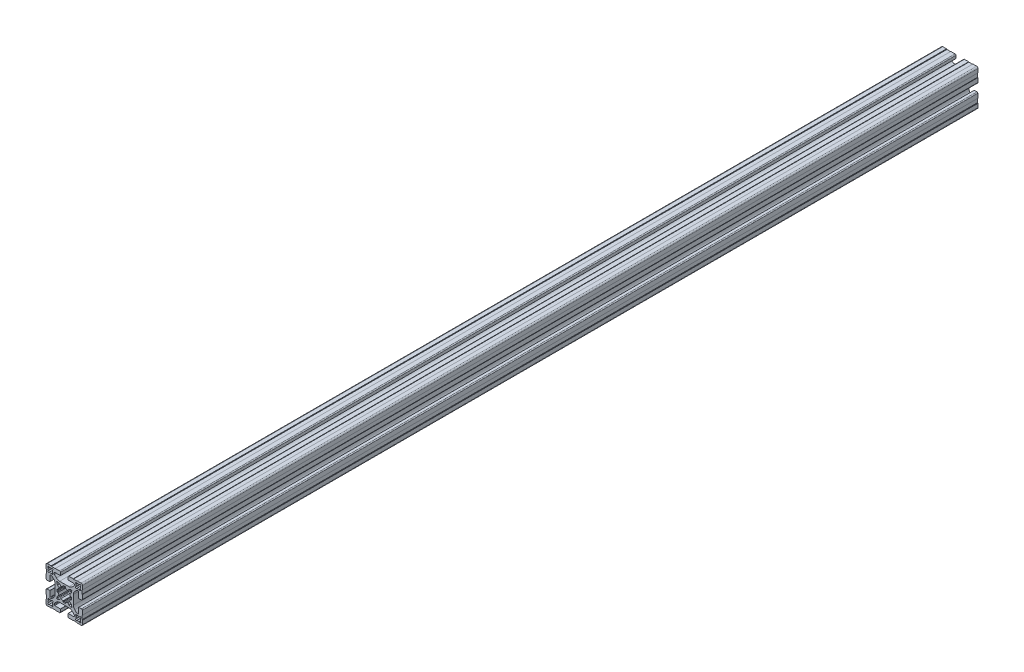
SolidWorks part; units mm, degrees
other "Item de detalhe1"
other "Item de detalhe2"
material "6063-T5"
ref_plane "Plano frontal" through (0, 0, 0) normal (0, 0, 1) x (1, 0, 0)
ref_plane "Plano superior" through (0, 0, 0) normal (0, 1, 0) x (1, 0, 0)
ref_plane "Plano direito" through (0, 0, 0) normal (1, 0, 0) x (0, 0, -1)
sketch "Esboço1" plane through (0, 0, 0) normal (0, 0, 1) x (1, 0, 0)
  point P0 (0, 0)
  line B0 (-5.3139, -7.6355) -> (-7.6488, -8.2611)
  arc B1 (-8.2611, -7.6488) -> (-7.6488, -8.2611) centre (-7.7782, -7.7782) ccw
  line B2 (-8.2611, -7.6488) -> (-7.6355, -5.3139)
  arc B3 (-7.4569, -5.0466) -> (-7.6355, -5.3139) centre (-7.1525, -5.4433) ccw
  line B4 (-7.4569, -5.0466) -> (-5.744, -3.7322)
  arc B5 (-6.7007, -1.4225) -> (-5.744, -3.7322) centre (0, 0) ccw
  line B6 (-6.7007, -1.4225) -> (-7.5204, -1.3146)
  arc B7 (-7.9522, -0.8735) -> (-7.5204, -1.3146) centre (-7.4552, -0.8189) ccw
  arc B8 (-7.9522, 0.8735) -> (-7.9522, -0.8735) centre (0, 0) ccw
  arc B9 (-7.5204, 1.3146) -> (-7.9522, 0.8735) centre (-7.4552, 0.8189) ccw
  line B10 (-7.5204, 1.3146) -> (-6.7007, 1.4225)
  arc B11 (-5.744, 3.7322) -> (-6.7007, 1.4225) centre (0, 0) ccw
  line B12 (-5.744, 3.7322) -> (-7.4569, 5.0466)
  arc B13 (-7.6355, 5.3139) -> (-7.4569, 5.0466) centre (-7.1525, 5.4433) ccw
  line B14 (-7.6355, 5.3139) -> (-8.2611, 7.6488)
  arc B15 (-7.6488, 8.2611) -> (-8.2611, 7.6488) centre (-7.7782, 7.7782) ccw
  line B16 (-7.6488, 8.2611) -> (-5.3139, 7.6355)
  arc B17 (-5.0466, 7.4569) -> (-5.3139, 7.6355) centre (-5.4433, 7.1525) ccw
  line B18 (-5.0466, 7.4569) -> (-3.7322, 5.744)
  arc B19 (-1.4225, 6.7007) -> (-3.7322, 5.744) centre (0, 0) ccw
  line B20 (-1.4225, 6.7007) -> (-1.3146, 7.5204)
  arc B21 (-0.8735, 7.9522) -> (-1.3146, 7.5204) centre (-0.8189, 7.4552) ccw
  arc B22 (0.8735, 7.9522) -> (-0.8735, 7.9522) centre (0, 0) ccw
  arc B23 (1.3146, 7.5204) -> (0.8735, 7.9522) centre (0.8189, 7.4552) ccw
  line B24 (1.3146, 7.5204) -> (1.4225, 6.7007)
  arc B25 (3.7322, 5.744) -> (1.4225, 6.7007) centre (0, 0) ccw
  line B26 (3.7322, 5.744) -> (5.0466, 7.4569)
  arc B27 (5.3139, 7.6355) -> (5.0466, 7.4569) centre (5.4433, 7.1525) ccw
  line B28 (5.3139, 7.6355) -> (7.6488, 8.2611)
  arc B29 (8.2611, 7.6488) -> (7.6488, 8.2611) centre (7.7782, 7.7782) ccw
  line B30 (8.2611, 7.6488) -> (7.6355, 5.3139)
  arc B31 (7.4569, 5.0466) -> (7.6355, 5.3139) centre (7.1525, 5.4433) ccw
  line B32 (7.4569, 5.0466) -> (5.744, 3.7322)
  arc B33 (6.7007, 1.4225) -> (5.744, 3.7322) centre (0, 0) ccw
  line B34 (6.7007, 1.4225) -> (7.5204, 1.3146)
  arc B35 (7.9522, 0.8735) -> (7.5204, 1.3146) centre (7.4552, 0.8189) ccw
  arc B36 (7.9522, -0.8735) -> (7.9522, 0.8735) centre (0, 0) ccw
  arc B37 (7.5204, -1.3146) -> (7.9522, -0.8735) centre (7.4552, -0.8189) ccw
  line B38 (7.5204, -1.3146) -> (6.7007, -1.4225)
  arc B39 (5.744, -3.7322) -> (6.7007, -1.4225) centre (0, 0) ccw
  line B40 (5.744, -3.7322) -> (7.4569, -5.0466)
  arc B41 (7.6355, -5.3139) -> (7.4569, -5.0466) centre (7.1525, -5.4433) ccw
  line B42 (7.6355, -5.3139) -> (8.2611, -7.6488)
  arc B43 (7.6488, -8.2611) -> (8.2611, -7.6488) centre (7.7782, -7.7782) ccw
  line B44 (7.6488, -8.2611) -> (5.3139, -7.6355)
  arc B45 (5.0466, -7.4569) -> (5.3139, -7.6355) centre (5.4433, -7.1525) ccw
  line B46 (5.0466, -7.4569) -> (3.7322, -5.744)
  arc B47 (1.4225, -6.7007) -> (3.7322, -5.744) centre (0, 0) ccw
  line B48 (1.4225, -6.7007) -> (1.3146, -7.5204)
  arc B49 (0.8735, -7.9522) -> (1.3146, -7.5204) centre (0.8189, -7.4552) ccw
  arc B50 (-0.8735, -7.9522) -> (0.8735, -7.9522) centre (0, 0) ccw
  arc B51 (-1.3146, -7.5204) -> (-0.8735, -7.9522) centre (-0.8189, -7.4552) ccw
  line B52 (-1.3146, -7.5204) -> (-1.4225, -6.7007)
  arc B53 (-3.7322, -5.744) -> (-1.4225, -6.7007) centre (0, 0) ccw
  line B54 (-3.7322, -5.744) -> (-5.0466, -7.4569)
  arc B55 (-5.3139, -7.6355) -> (-5.0466, -7.4569) centre (-5.4433, -7.1525) ccw
  line B56 (21, 0) -> (-21, 0) construction
  line B57 (-17.8572, 16.7966) -> (-17.4167, 16.356)
  arc B58 (-16.7966, 17.8572) -> (-17.8572, 16.7966) centre (-17.3269, 17.3269) ccw
  line B59 (-16.356, 17.4167) -> (-16.7966, 17.8572)
  arc B60 (-14.044, 17.4167) -> (-16.356, 17.4167) centre (-15.2, 15.2) ccw
  line B61 (-13.6034, 17.8572) -> (-14.044, 17.4167)
  arc B62 (-12.5428, 16.7966) -> (-13.6034, 17.8572) centre (-13.0731, 17.3269) ccw
  line B63 (-12.9833, 16.356) -> (-12.5428, 16.7966)
  arc B64 (-12.9833, 14.044) -> (-12.9833, 16.356) centre (-15.2, 15.2) ccw
  line B65 (-12.5428, 13.6034) -> (-12.9833, 14.044)
  arc B66 (-13.6034, 12.5428) -> (-12.5428, 13.6034) centre (-13.0731, 13.0731) ccw
  line B67 (-14.044, 12.9833) -> (-13.6034, 12.5428)
  arc B68 (-16.356, 12.9833) -> (-14.044, 12.9833) centre (-15.2, 15.2) ccw
  line B69 (-16.7966, 12.5428) -> (-16.356, 12.9833)
  arc B70 (-17.8572, 13.6034) -> (-16.7966, 12.5428) centre (-17.3269, 13.0731) ccw
  line B71 (-17.4167, 14.044) -> (-17.8572, 13.6034)
  arc B72 (-17.4167, 16.356) -> (-17.4167, 14.044) centre (-15.2, 15.2) ccw
  line B73 (17.4167, 14.044) -> (17.8572, 13.6034)
  arc B74 (16.7966, 12.5428) -> (17.8572, 13.6034) centre (17.3269, 13.0731) ccw
  line B75 (16.7966, 12.5428) -> (16.356, 12.9833)
  arc B76 (14.044, 12.9833) -> (16.356, 12.9833) centre (15.2, 15.2) ccw
  line B77 (14.044, 12.9833) -> (13.6034, 12.5428)
  arc B78 (12.5428, 13.6034) -> (13.6034, 12.5428) centre (13.0731, 13.0731) ccw
  line B79 (12.5428, 13.6034) -> (12.9833, 14.044)
  arc B80 (12.9833, 16.356) -> (12.9833, 14.044) centre (15.2, 15.2) ccw
  line B81 (12.9833, 16.356) -> (12.5428, 16.7966)
  arc B82 (13.6034, 17.8572) -> (12.5428, 16.7966) centre (13.0731, 17.3269) ccw
  line B83 (13.6034, 17.8572) -> (14.044, 17.4167)
  arc B84 (16.356, 17.4167) -> (14.044, 17.4167) centre (15.2, 15.2) ccw
  line B85 (16.356, 17.4167) -> (16.7966, 17.8572)
  arc B86 (17.8572, 16.7966) -> (16.7966, 17.8572) centre (17.3269, 17.3269) ccw
  line B87 (17.8572, 16.7966) -> (17.4167, 16.356)
  arc B88 (17.4167, 14.044) -> (17.4167, 16.356) centre (15.2, 15.2) ccw
  line B89 (-17.4167, -14.044) -> (-17.8572, -13.6034)
  arc B90 (-16.7966, -12.5428) -> (-17.8572, -13.6034) centre (-17.3269, -13.0731) ccw
  line B91 (-16.7966, -12.5428) -> (-16.356, -12.9833)
  arc B92 (-14.044, -12.9833) -> (-16.356, -12.9833) centre (-15.2, -15.2) ccw
  line B93 (-14.044, -12.9833) -> (-13.6034, -12.5428)
  arc B94 (-12.5428, -13.6034) -> (-13.6034, -12.5428) centre (-13.0731, -13.0731) ccw
  line B95 (-12.5428, -13.6034) -> (-12.9833, -14.044)
  arc B96 (-12.9833, -16.356) -> (-12.9833, -14.044) centre (-15.2, -15.2) ccw
  line B97 (-12.9833, -16.356) -> (-12.5428, -16.7966)
  arc B98 (-13.6034, -17.8572) -> (-12.5428, -16.7966) centre (-13.0731, -17.3269) ccw
  line B99 (-13.6034, -17.8572) -> (-14.044, -17.4167)
  arc B100 (-16.356, -17.4167) -> (-14.044, -17.4167) centre (-15.2, -15.2) ccw
  line B101 (-16.356, -17.4167) -> (-16.7966, -17.8572)
  arc B102 (-17.8572, -16.7966) -> (-16.7966, -17.8572) centre (-17.3269, -17.3269) ccw
  line B103 (-17.8572, -16.7966) -> (-17.4167, -16.356)
  arc B104 (-17.4167, -14.044) -> (-17.4167, -16.356) centre (-15.2, -15.2) ccw
  line B105 (17.8572, -16.7966) -> (17.4167, -16.356)
  arc B106 (16.7966, -17.8572) -> (17.8572, -16.7966) centre (17.3269, -17.3269) ccw
  line B107 (16.356, -17.4167) -> (16.7966, -17.8572)
  arc B108 (14.044, -17.4167) -> (16.356, -17.4167) centre (15.2, -15.2) ccw
  line B109 (13.6034, -17.8572) -> (14.044, -17.4167)
  arc B110 (12.5428, -16.7966) -> (13.6034, -17.8572) centre (13.0731, -17.3269) ccw
  line B111 (12.9833, -16.356) -> (12.5428, -16.7966)
  arc B112 (12.9833, -14.044) -> (12.9833, -16.356) centre (15.2, -15.2) ccw
  line B113 (12.5428, -13.6034) -> (12.9833, -14.044)
  arc B114 (13.6034, -12.5428) -> (12.5428, -13.6034) centre (13.0731, -13.0731) ccw
  line B115 (14.044, -12.9833) -> (13.6034, -12.5428)
  arc B116 (16.356, -12.9833) -> (14.044, -12.9833) centre (15.2, -15.2) ccw
  line B117 (16.7966, -12.5428) -> (16.356, -12.9833)
  arc B118 (17.8572, -13.6034) -> (16.7966, -12.5428) centre (17.3269, -13.0731) ccw
  line B119 (17.4167, -14.044) -> (17.8572, -13.6034)
  arc B120 (17.4167, -16.356) -> (17.4167, -14.044) centre (15.2, -15.2) ccw
  line B121 (4.15, -18.8) -> (4.15, -15.9)
  arc B122 (4.25, -15.8) -> (4.15, -15.9) centre (4.25, -15.9) ccw
  line B123 (4.25, -15.8) -> (10.5, -15.8)
  arc B124 (10.5, -15.8) -> (11, -15.3) centre (10.5, -15.3) ccw
  line B125 (11, -15.3) -> (11, -14.4497)
  arc B126 (11, -14.4497) -> (10.5607, -13.3891) centre (9.5, -14.4497) ccw
  line B127 (10.5607, -13.3891) -> (8.636, -11.4645)
  arc B128 (8.636, -11.4645) -> (5.1005, -10) centre (5.1005, -15) ccw
  line B129 (5.1005, -10) -> (0, -10)
  line B130 (0, -10) -> (-5.1005, -10)
  arc B131 (-5.1005, -10) -> (-8.636, -11.4645) centre (-5.1005, -15) ccw
  line B132 (-8.636, -11.4645) -> (-10.5607, -13.3891)
  arc B133 (-10.5607, -13.3891) -> (-11, -14.4497) centre (-9.5, -14.4497) ccw
  line B134 (-11, -14.4497) -> (-11, -15.3)
  arc B135 (-11, -15.3) -> (-10.5, -15.8) centre (-10.5, -15.3) ccw
  line B136 (-10.5, -15.8) -> (-4.25, -15.8)
  arc B137 (-4.15, -15.9) -> (-4.25, -15.8) centre (-4.25, -15.9) ccw
  line B138 (-4.15, -15.9) -> (-4.15, -18.8)
  arc B139 (-5.15, -19.8) -> (-4.15, -18.8) centre (-5.15, -18.8) ccw
  line B140 (-5.15, -19.8) -> (-9.8, -19.8)
  line B141 (-9.8, -19.8) -> (-10, -19.6)
  line B142 (-10, -19.6) -> (-14, -19.6)
  line B143 (-14, -19.6) -> (-14.4, -20)
  line B144 (-14.4, -20) -> (-18.5, -20)
  arc B145 (-20, -18.5) -> (-18.5, -20) centre (-18.5, -18.5) ccw
  line B146 (-20, -18.5) -> (-20, -14.4)
  line B147 (-20, -14.4) -> (-19.6, -14)
  line B148 (-19.6, -14) -> (-19.6, -10)
  line B149 (-19.6, -10) -> (-19.8, -9.8)
  line B150 (-19.8, -9.8) -> (-19.8, -5.15)
  arc B151 (-18.8, -4.15) -> (-19.8, -5.15) centre (-18.8, -5.15) ccw
  line B152 (-18.8, -4.15) -> (-15.9, -4.15)
  arc B153 (-15.8, -4.25) -> (-15.9, -4.15) centre (-15.9, -4.25) ccw
  line B154 (-15.8, -4.25) -> (-15.8, -10.5)
  arc B155 (-15.8, -10.5) -> (-15.3, -11) centre (-15.3, -10.5) ccw
  line B156 (-15.3, -11) -> (-14.4497, -11)
  arc B157 (-14.4497, -11) -> (-13.3891, -10.5607) centre (-14.4497, -9.5) ccw
  line B158 (-13.3891, -10.5607) -> (-11.4645, -8.636)
  arc B159 (-11.4645, -8.636) -> (-10, -5.1005) centre (-15, -5.1005) ccw
  line B160 (-10, -5.1005) -> (-10, 0)
  line B161 (-10, 0) -> (-10, 5.1005)
  arc B162 (-10, 5.1005) -> (-11.4645, 8.636) centre (-15, 5.1005) ccw
  line B163 (-11.4645, 8.636) -> (-13.3891, 10.5607)
  arc B164 (-13.3891, 10.5607) -> (-14.4497, 11) centre (-14.4497, 9.5) ccw
  line B165 (-14.4497, 11) -> (-15.3, 11)
  arc B166 (-15.3, 11) -> (-15.8, 10.5) centre (-15.3, 10.5) ccw
  line B167 (-15.8, 10.5) -> (-15.8, 4.25)
  arc B168 (-15.9, 4.15) -> (-15.8, 4.25) centre (-15.9, 4.25) ccw
  line B169 (-15.9, 4.15) -> (-18.8, 4.15)
  arc B170 (-19.8, 5.15) -> (-18.8, 4.15) centre (-18.8, 5.15) ccw
  line B171 (-19.8, 5.15) -> (-19.8, 9.8)
  line B172 (-19.8, 9.8) -> (-19.6, 10)
  line B173 (-19.6, 10) -> (-19.6, 14)
  line B174 (-19.6, 14) -> (-20, 14.4)
  line B175 (-20, 14.4) -> (-20, 18.5)
  arc B176 (-18.5, 20) -> (-20, 18.5) centre (-18.5, 18.5) ccw
  line B177 (-18.5, 20) -> (-14.4, 20)
  line B178 (-14.4, 20) -> (-14, 19.6)
  line B179 (-14, 19.6) -> (-10, 19.6)
  line B180 (-10, 19.6) -> (-9.8, 19.8)
  line B181 (-9.8, 19.8) -> (-5.15, 19.8)
  arc B182 (-4.15, 18.8) -> (-5.15, 19.8) centre (-5.15, 18.8) ccw
  line B183 (-4.15, 18.8) -> (-4.15, 15.9)
  arc B184 (-4.25, 15.8) -> (-4.15, 15.9) centre (-4.25, 15.9) ccw
  line B185 (-4.25, 15.8) -> (-10.5, 15.8)
  arc B186 (-10.5, 15.8) -> (-11, 15.3) centre (-10.5, 15.3) ccw
  line B187 (-11, 15.3) -> (-11, 14.4497)
  arc B188 (-11, 14.4497) -> (-10.5607, 13.3891) centre (-9.5, 14.4497) ccw
  line B189 (-10.5607, 13.3891) -> (-8.636, 11.4645)
  arc B190 (-8.636, 11.4645) -> (-5.1005, 10) centre (-5.1005, 15) ccw
  line B191 (-5.1005, 10) -> (0, 10)
  line B192 (0, 10) -> (5.1005, 10)
  arc B193 (5.1005, 10) -> (8.636, 11.4645) centre (5.1005, 15) ccw
  line B194 (8.636, 11.4645) -> (10.5607, 13.3891)
  arc B195 (10.5607, 13.3891) -> (11, 14.4497) centre (9.5, 14.4497) ccw
  line B196 (11, 14.4497) -> (11, 15.3)
  arc B197 (11, 15.3) -> (10.5, 15.8) centre (10.5, 15.3) ccw
  line B198 (10.5, 15.8) -> (4.25, 15.8)
  arc B199 (4.15, 15.9) -> (4.25, 15.8) centre (4.25, 15.9) ccw
  line B200 (4.15, 15.9) -> (4.15, 18.8)
  arc B201 (5.15, 19.8) -> (4.15, 18.8) centre (5.15, 18.8) ccw
  line B202 (5.15, 19.8) -> (9.8, 19.8)
  line B203 (9.8, 19.8) -> (10, 19.6)
  line B204 (10, 19.6) -> (14, 19.6)
  line B205 (14, 19.6) -> (14.4, 20)
  line B206 (14.4, 20) -> (18.5, 20)
  arc B207 (20, 18.5) -> (18.5, 20) centre (18.5, 18.5) ccw
  line B208 (20, 18.5) -> (20, 14.4)
  line B209 (20, 14.4) -> (19.6, 14)
  line B210 (19.6, 14) -> (19.6, 10)
  line B211 (19.6, 10) -> (19.8, 9.8)
  line B212 (19.8, 9.8) -> (19.8, 5.15)
  arc B213 (18.8, 4.15) -> (19.8, 5.15) centre (18.8, 5.15) ccw
  line B214 (18.8, 4.15) -> (15.9, 4.15)
  arc B215 (15.8, 4.25) -> (15.9, 4.15) centre (15.9, 4.25) ccw
  line B216 (15.8, 4.25) -> (15.8, 10.5)
  arc B217 (15.8, 10.5) -> (15.3, 11) centre (15.3, 10.5) ccw
  line B218 (15.3, 11) -> (14.4497, 11)
  arc B219 (14.4497, 11) -> (13.3891, 10.5607) centre (14.4497, 9.5) ccw
  line B220 (13.3891, 10.5607) -> (11.4645, 8.636)
  arc B221 (11.4645, 8.636) -> (10, 5.1005) centre (15, 5.1005) ccw
  line B222 (10, 5.1005) -> (10, 0)
  line B223 (10, 0) -> (10, -5.1005)
  arc B224 (10, -5.1005) -> (11.4645, -8.636) centre (15, -5.1005) ccw
  line B225 (11.4645, -8.636) -> (13.3891, -10.5607)
  arc B226 (13.3891, -10.5607) -> (14.4497, -11) centre (14.4497, -9.5) ccw
  line B227 (14.4497, -11) -> (15.3, -11)
  arc B228 (15.3, -11) -> (15.8, -10.5) centre (15.3, -10.5) ccw
  line B229 (15.8, -10.5) -> (15.8, -4.25)
  arc B230 (15.9, -4.15) -> (15.8, -4.25) centre (15.9, -4.25) ccw
  line B231 (15.9, -4.15) -> (18.8, -4.15)
  arc B232 (19.8, -5.15) -> (18.8, -4.15) centre (18.8, -5.15) ccw
  line B233 (19.8, -5.15) -> (19.8, -9.8)
  line B234 (19.8, -9.8) -> (19.6, -10)
  line B235 (19.6, -10) -> (19.6, -14)
  line B236 (19.6, -14) -> (20, -14.4)
  line B237 (20, -14.4) -> (20, -18.5)
  arc B238 (18.5, -20) -> (20, -18.5) centre (18.5, -18.5) ccw
  line B239 (18.5, -20) -> (14.4, -20)
  line B240 (14.4, -20) -> (14, -19.6)
  line B241 (14, -19.6) -> (10, -19.6)
  line B242 (10, -19.6) -> (9.8, -19.8)
  line B243 (9.8, -19.8) -> (5.15, -19.8)
  arc B244 (4.15, -18.8) -> (5.15, -19.8) centre (5.15, -18.8) ccw
sketch_block_instance "P40103-1"
sketch_block "P40103"
other "Item de detalhe3"
other "Item de detalhe4"
extrude "Ressalto-extrusão1" add sketch "Esboço1" along normal mid plane 980
